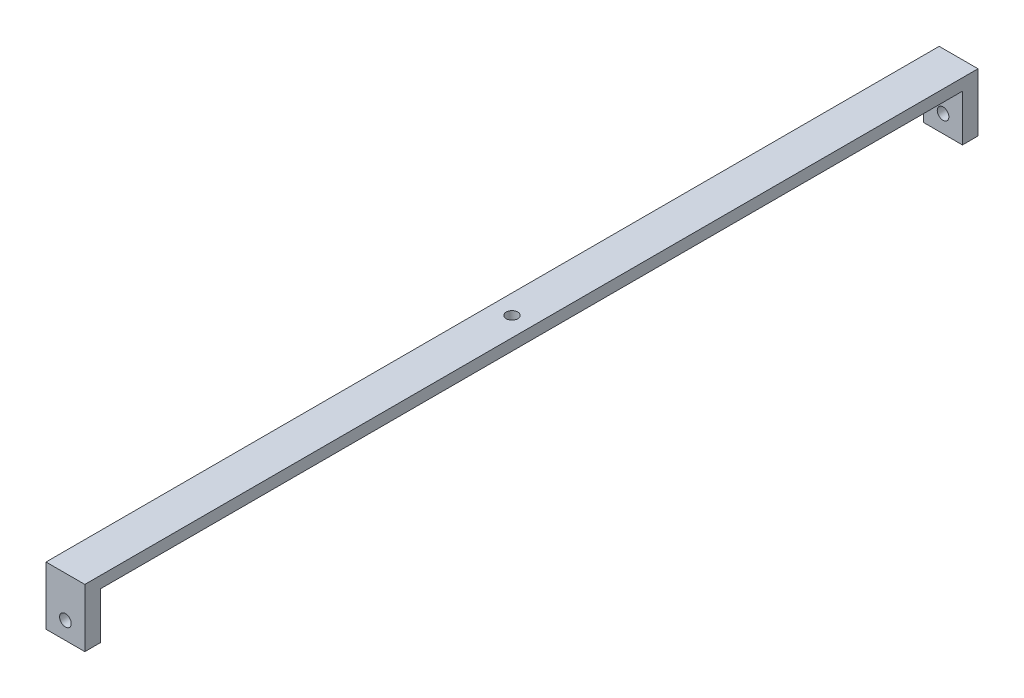
SolidWorks part; units mm, degrees
material "Aleación 1060"
ref_plane "Alzado" through (0, 0, 0) normal (0, 0, 1) x (1, 0, 0)
ref_plane "Planta" through (0, 0, 0) normal (0, 1, 0) x (1, 0, 0)
ref_plane "Vista lateral" through (0, 0, 0) normal (1, 0, 0) x (0, 0, -1)
sketch "Croquis1" plane through (0, 0, 0) normal (0, 0, 1) x (1, 0, 0)
  line L0 (0, 7.5) -> (0, -7.5) construction
  line L1 (-5, -7.5) -> (5, -7.5)
  line L2 (-5, -7.5) -> (-5, 7.5)
  line L3 (-5, 7.5) -> (5, 7.5)
  line L4 (5, -7.5) -> (5, 7.5)
  line L5 (-5, -7.5) -> (5, 7.5) construction
  line L6 (-5, 7.5) -> (5, -7.5) construction
  circle A1 centre (0, -3) radius 1.5
  point P0 (0, 0)
  dimension "D2" = 3
  dimension "D4" = 10.5
  dimension "D1" = 10
  dimension "D3" = 15
extrude "Saliente-Extruir1" add sketch "Croquis1" along normal mid plane 230
sketch "Croquis2" plane through (-5, 0, 0) normal (-1, 0, 0) x (0, 0, 1)
  line L0 (115, -7.5) -> (-115, -7.5) construction
  line L1 (111, -7.5) -> (-111, -7.5)
  line L2 (111, -7.5) -> (111, 4.5)
  line L3 (111, 4.5) -> (-111, 4.5)
  line L4 (-111, -7.5) -> (-111, 4.5)
  line L5 (115, 7.5) -> (-115, 7.5) construction
  line L6 (-115, 7.5) -> (-115, -7.5) construction
  line L7 (115, 7.5) -> (115, -7.5) construction
  dimension "D1" = 3
  dimension "D2" = 4
  dimension "D3" = 4
extrude "Cortar-Extruir1" cut sketch "Croquis2" against normal through all
sketch "Croquis3" plane through (0, 7.5, 0) normal (0, 1, 0) x (1, 0, 0)
  circle A0 centre (0, 0) radius 1.5
  dimension "D1" = 3
extrude "Cortar-Extruir2" cut sketch "Croquis3" against normal blind 10
